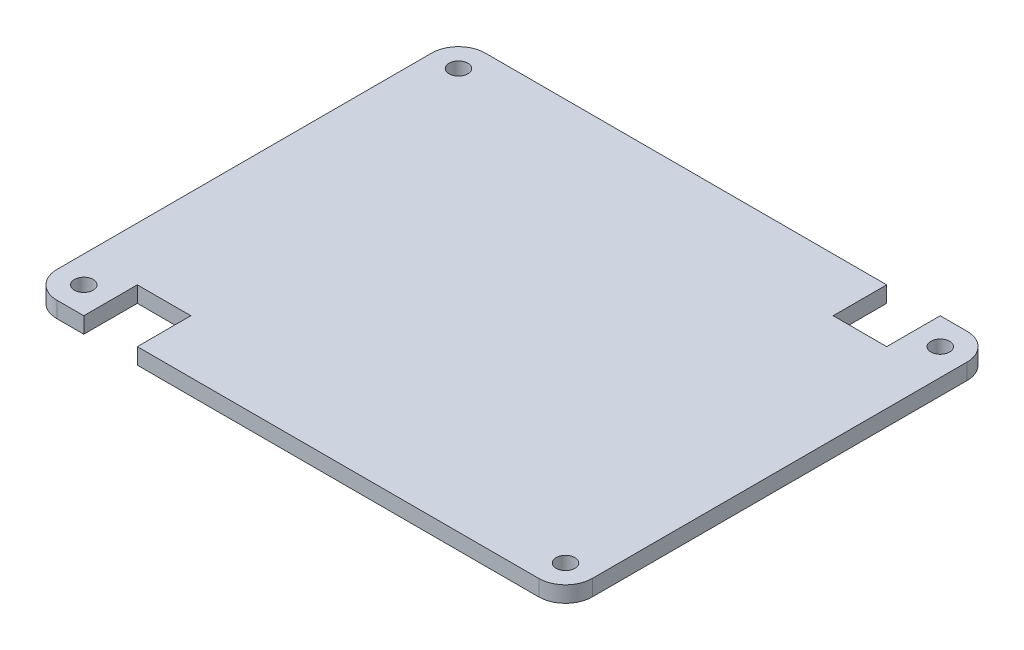
SolidWorks part; units mm, degrees
ref_plane "Front Plane" through (0, 0, 0) normal (0, 0, 1) x (1, 0, 0)
ref_plane "Top Plane" through (0, 0, 0) normal (0, 1, 0) x (1, 0, 0)
ref_plane "Right Plane" through (0, 0, 0) normal (1, 0, 0) x (0, 0, -1)
sketch "Sketch1" plane through (0, 0, 0) normal (0, 1, 0) x (1, 0, 0)
  line L1 (-45, 40) -> (45, 40)
  line L2 (-50, 35) -> (-50, -35)
  line L3 (-45, -40) -> (45, -40)
  line L4 (50, 35) -> (50, -35)
  line L5 (-50, 40) -> (50, -40) construction
  line L6 (-50, -40) -> (50, 40) construction
  arc A0 (45, 40) -> (50, 35) centre (45, 35) cw
  arc A1 (45, -40) -> (50, -35) centre (45, -35) ccw
  arc A2 (-50, -35) -> (-45, -40) centre (-45, -35) ccw
  arc A3 (-45, 40) -> (-50, 35) centre (-45, 35) ccw
  point P0 (0, 0)
  dimension "D3" = 5
  dimension "D1" = 100
  dimension "D2" = 80
extrude "Boss-Extrude1" add sketch "Sketch1" along normal blind 3
sketch "Sketch3" plane through (0, 3, 0) normal (0, 1, 0) x (1, 0, 0)
  line L0 (-45, -40) -> (45, -40) construction
  line L1 (-50, 35) -> (-50, -35) construction
  circle A0 centre (-45, -35) radius 1.75
  dimension "D1" = 3.5
  dimension "D2" = 5
  dimension "D3" = 5
extrude "Cut-Extrude2" cut sketch "Sketch3" against normal through all
pattern_linear "LPattern1" count 2 spacing 70 along (0, 0, -1) count 2 spacing 90 along (1, 0, 0) of "Cut-Extrude2"
sketch "Sketch5" plane through (0, 3, 0) normal (0, 1, 0) x (1, 0, 0)
  line L0 (-45, -40) -> (45, -40) construction
  line L1 (-40, -40) -> (-30, -40)
  line L2 (-40, -40) -> (-40, -30)
  line L3 (-40, -30) -> (-30, -30)
  line L4 (-30, -40) -> (-30, -30)
  line L5 (45, 40) -> (-45, 40) construction
  line L6 (30, 40) -> (40, 40)
  line L7 (30, 40) -> (30, 30)
  line L8 (30, 30) -> (40, 30)
  line L9 (40, 40) -> (40, 30)
  line L10 (-50, 35) -> (-50, -35) construction
  line L11 (50, -35) -> (50, 35) construction
  dimension "D1" = 10
  dimension "D2" = 10
  dimension "D3" = 10
  dimension "D4" = 10
  dimension "D5" = 10
  dimension "D6" = 10
extrude "Cut-Extrude4" cut sketch "Sketch5" against normal through all
